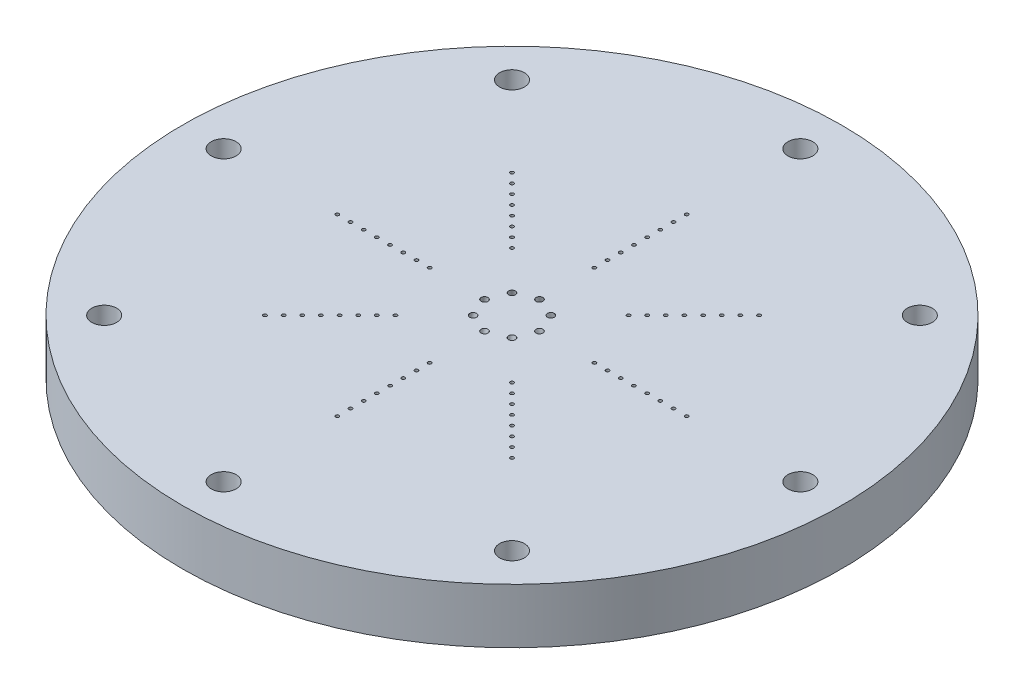
SolidWorks part; units mm, degrees
ref_plane "Front Plane" through (0, 0, 0) normal (0, 0, 1) x (1, 0, 0)
ref_plane "Top Plane" through (0, 0, 0) normal (0, 1, 0) x (1, 0, 0)
ref_plane "Right Plane" through (0, 0, 0) normal (1, 0, 0) x (0, 0, -1)
sketch "Sketch1" plane through (0, 0, 0) normal (0, 1, 0) x (1, 0, 0)
  circle A0 centre (0, 0) radius 38.1
  dimension "D1" = 76.2
extrude "Boss-Extrude1" add sketch "Sketch1" along normal blind 6.35
sketch "Sketch2" plane through (0, 0, 0) normal (0, -1, 0) x (1, 0, 0)
  circle A0 centre (0, 0) radius 33.3375
  circle A1 centre (0, 33.3375) radius 0.762
  dimension "D1" = 66.675
hole_wizard "CBORE for #4 Button Head Cap Screw1" positions "Sketch5" profile "Sketch4" counterbore size "#4" standard "ANSI Inch" end condition through all
sketch "Sketch5" plane through (0, 0, 0) normal (0, -1, 0) x (-1, 0, 0)
  point P0 (0, -33.3375)
sketch "Sketch4" plane through (0, 0, 33.3375) normal (1, 0, 0) x (0, 0, -1)
  line L0 (0, 0) -> (0, 6.35)
  line L1 (0, 6.35) -> (1.4351, 6.35)
  line L3 (1.4351, 6.35) -> (1.4351, 1.905)
  line L4 (1.4351, 1.905) -> (2.413, 1.905)
  line L5 (2.413, 1.905) -> (2.413, 0)
  line L7 (2.413, 0) -> (0, 0)
  line L11 (0, -6.35) -> (0, 107.95) construction
  dimension "Thru Hole Dia." = 2.8702
  dimension "Thru Hole Depth" = 6.35
  dimension "C'Bore Dia." = 4.826
  dimension "C'Bore Depth" = 1.905
pattern_circular "CirPattern1" count 8 over 360 about axis through (0, 0, 0) along (0, 1, 0) of "CBORE for #4 Button Head Cap Screw1"
sketch "Sketch6" plane through (0, 6.35, 0) normal (0, 1, 0) x (1, 0, 0)
  line L0 (0, 9.525) -> (0, 11.1125) construction
  line L1 (0, 9.525) -> (0, 11.049) construction
  circle A0 centre (0, 9.525) radius 0.1984
  circle A19 centre (0, 11.049) radius 0.1984
  circle A20 centre (0, 12.573) radius 0.1984
  circle A21 centre (0, 14.097) radius 0.1984
  circle A22 centre (0, 15.621) radius 0.1984
  circle A23 centre (0, 17.145) radius 0.1984
  circle A24 centre (0, 18.669) radius 0.1984
  circle A25 centre (0, 20.193) radius 0.1984
  circle A26 centre (6.7352, 6.7352) radius 0.1984
  circle A27 centre (7.8128, 7.8128) radius 0.1984
  circle A28 centre (8.8905, 8.8905) radius 0.1984
  circle A29 centre (9.9681, 9.9681) radius 0.1984
  circle A30 centre (11.0457, 11.0457) radius 0.1984
  circle A31 centre (12.1233, 12.1233) radius 0.1984
  circle A32 centre (13.201, 13.201) radius 0.1984
  circle A33 centre (14.2786, 14.2786) radius 0.1984
  circle A34 centre (9.525, 0) radius 0.1984
  circle A35 centre (11.049, 0) radius 0.1984
  circle A36 centre (12.573, 0) radius 0.1984
  circle A37 centre (14.097, 0) radius 0.1984
  circle A38 centre (15.621, 0) radius 0.1984
  circle A39 centre (17.145, 0) radius 0.1984
  circle A40 centre (18.669, 0) radius 0.1984
  circle A41 centre (20.193, 0) radius 0.1984
  circle A42 centre (6.7352, -6.7352) radius 0.1984
  circle A43 centre (7.8128, -7.8128) radius 0.1984
  circle A44 centre (8.8905, -8.8905) radius 0.1984
  circle A45 centre (9.9681, -9.9681) radius 0.1984
  circle A46 centre (11.0457, -11.0457) radius 0.1984
  circle A47 centre (12.1233, -12.1233) radius 0.1984
  circle A48 centre (13.201, -13.201) radius 0.1984
  circle A49 centre (14.2786, -14.2786) radius 0.1984
  circle A50 centre (0, -9.525) radius 0.1984
  circle A51 centre (0, -11.049) radius 0.1984
  circle A52 centre (0, -12.573) radius 0.1984
  circle A53 centre (0, -14.097) radius 0.1984
  circle A54 centre (0, -15.621) radius 0.1984
  circle A55 centre (0, -17.145) radius 0.1984
  circle A56 centre (0, -18.669) radius 0.1984
  circle A57 centre (0, -20.193) radius 0.1984
  circle A58 centre (-6.7352, -6.7352) radius 0.1984
  circle A59 centre (-7.8128, -7.8128) radius 0.1984
  circle A60 centre (-8.8905, -8.8905) radius 0.1984
  circle A61 centre (-9.9681, -9.9681) radius 0.1984
  circle A62 centre (-11.0457, -11.0457) radius 0.1984
  circle A63 centre (-12.1233, -12.1233) radius 0.1984
  circle A64 centre (-13.201, -13.201) radius 0.1984
  circle A65 centre (-14.2786, -14.2786) radius 0.1984
  circle A66 centre (-9.525, 0) radius 0.1984
  circle A67 centre (-11.049, 0) radius 0.1984
  circle A68 centre (-12.573, 0) radius 0.1984
  circle A69 centre (-14.097, 0) radius 0.1984
  circle A70 centre (-15.621, 0) radius 0.1984
  circle A71 centre (-17.145, 0) radius 0.1984
  circle A72 centre (-18.669, 0) radius 0.1984
  circle A73 centre (-20.193, 0) radius 0.1984
  circle A74 centre (-6.7352, 6.7352) radius 0.1984
  circle A75 centre (-7.8128, 7.8128) radius 0.1984
  circle A76 centre (-8.8905, 8.8905) radius 0.1984
  circle A77 centre (-9.9681, 9.9681) radius 0.1984
  circle A78 centre (-11.0457, 11.0457) radius 0.1984
  circle A79 centre (-12.1233, 12.1233) radius 0.1984
  circle A80 centre (-13.201, 13.201) radius 0.1984
  circle A81 centre (-14.2786, 14.2786) radius 0.1984
  point P135 (0, 0)
  dimension "D1" = 0.3969
  dimension "D2" = 1.5875
  dimension "D3" = 1.524
  dimension "D4" = 8
extrude "Cut-Extrude1" cut sketch "Sketch6" against normal through all
sketch "Sketch7" plane through (0, 6.35, 0) normal (0, 1, 0) x (1, 0, 0)
  circle A0 centre (0, 3.175) radius 0.3969
  dimension "D1" = 3.175
  dimension "D2" = 0.7937
sketch "Sketch8" plane through (0, 0, 0) normal (0, -1, 0) x (1, 0, 0)
  circle A0 centre (0, -4.7625) radius 0.3969
  circle A1 centre (0, -3.175) radius 0.3969 construction
  dimension "D1" = 0.7937
  dimension "D2" = 1.5875
sketch3d "3DSketch3"
  line L0 (0, 6.35, -3.175) -> (0, 0, -4.7625)
sweep "Cut-Sweep1" cut profiles "Sketch7" path "3DSketch3"
pattern_circular "CirPattern2" count 8 over 360 about axis through (0, 6.35, 0) along (0, 1, 0) of "Cut-Sweep1"
